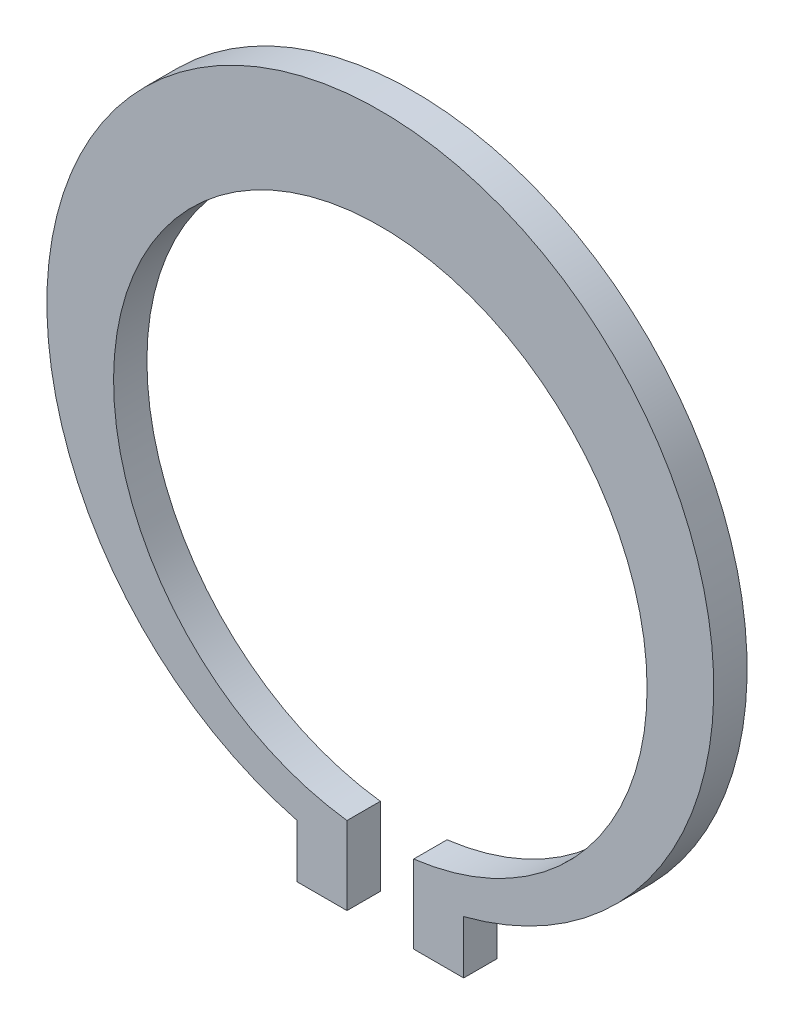
SolidWorks part; units mm, degrees
ref_plane "Front Plane" through (0, 0, 0) normal (0, 0, 1) x (1, 0, 0)
ref_plane "Top Plane" through (0, 0, 0) normal (0, 1, 0) x (1, 0, 0)
ref_plane "Right Plane" through (0, 0, 0) normal (1, 0, 0) x (0, 0, -1)
sketch "Sketch2" plane through (0, 0, 0) normal (0, 0, 1) x (1, 0, 0)
  line L0 (0, -18) -> (0, -26.2547) construction
  line L1 (2, -17.8745) -> (2, -22.5545)
  line L2 (2, -22.5545) -> (5, -22.5545)
  line L3 (5, -22.5545) -> (5, -19.3649)
  line L4 (-2, -17.8745) -> (-2, -22.5545)
  line L5 (-2, -22.5545) -> (-5, -22.5545)
  line L6 (-5, -22.5545) -> (-5, -19.3649)
  line L7 (5, -17.1987) -> (5, -14.2999) construction
  arc A0 (0, -20) -> (2, -19.8997) centre (0, 0) ccw
  arc A1 (2, -17.8745) -> (-2, -17.8745) centre (0, -2) ccw
  arc A2 (5, -19.3649) -> (-5, -19.3649) centre (0, 0) ccw
  point P7 (2, -20.2145)
  dimension "D1" = 40
  dimension "D2" = 32
  dimension "D3" = 2
  dimension "D4" = 4.68
  dimension "D5" = 2
  dimension "D6" = 3
  dimension "D7" = 5
extrude "Boss-Extrude1" add sketch "Sketch2" along normal blind 2 contours L3 A2 L6 L5 L4 A1 L1 L2
